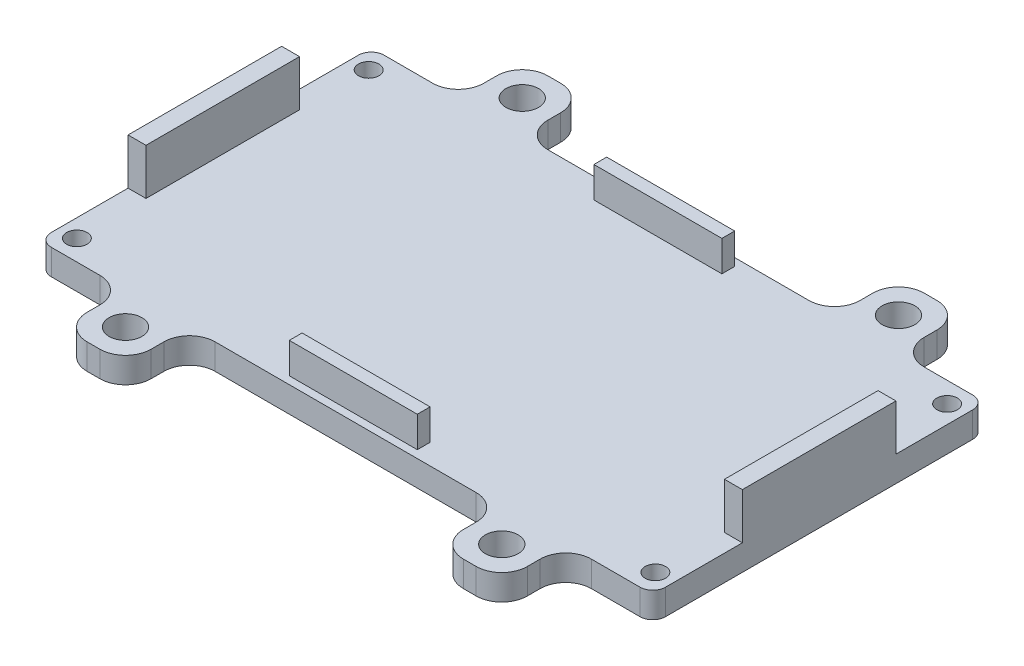
SolidWorks part; units mm, degrees
ref_plane "Front" through (0, 0, 0) normal (0, 0, 1) x (1, 0, 0)
ref_plane "Top" through (0, 0, 0) normal (0, 1, 0) x (1, 0, 0)
ref_plane "Right" through (0, 0, 0) normal (1, 0, 0) x (0, 0, -1)
sketch "草图1" plane through (0, 0, 0) normal (0, 1, 0) x (1, 0, 0)
  line L1 (-60, -32.5) -> (60, -32.5)
  line L2 (-60, -32.5) -> (-60, 32.5)
  line L3 (-60, 32.5) -> (60, 32.5)
  line L4 (60, -32.5) -> (60, 32.5)
  line L5 (-60, -32.5) -> (60, 32.5) construction
  line L6 (-60, 32.5) -> (60, -32.5) construction
  point P0 (0, 0)
  dimension "D1" = 120
  dimension "D2" = 65
extrude "凸台-拉伸1" add sketch "草图1" along normal blind 5
sketch "草图2" plane through (0, 5, 0) normal (0, 1, 0) x (1, 0, 0)
  line L0 (60, 32.5) -> (-60, 32.5) construction
  line L1 (-43, 32.5) -> (-30.5, 32.5)
  line L2 (-43, 32.5) -> (-43, 45)
  line L3 (-43, 45) -> (-30.5, 45)
  line L4 (-30.5, 32.5) -> (-30.5, 45)
  line L5 (-60, 32.5) -> (-60, -32.5) construction
  line L6 (0, 51.1348) -> (0, -43.6514) construction
  line L7 (-74.3344, 0) -> (82.9175, 0) construction
  line L8 (30.5, 32.5) -> (30.5, 45)
  line L9 (43, 32.5) -> (30.5, 32.5)
  line L10 (43, 45) -> (30.5, 45)
  line L11 (43, 32.5) -> (43, 45)
  line L12 (43, -32.5) -> (43, -45)
  line L13 (43, -45) -> (30.5, -45)
  line L14 (43, -32.5) -> (30.5, -32.5)
  line L15 (30.5, -32.5) -> (30.5, -45)
  line L16 (-30.5, -32.5) -> (-30.5, -45)
  line L17 (-43, -45) -> (-30.5, -45)
  line L18 (-43, -32.5) -> (-43, -45)
  line L19 (-43, -32.5) -> (-30.5, -32.5)
  dimension "D1" = 12.5
  dimension "D2" = 12.5
  dimension "D3" = 17
extrude "凸台-拉伸2" add sketch "草图2" against normal blind 5
sketch "草图3" plane through (0, 5, 0) normal (0, 1, 0) x (1, 0, 0)
  line L0 (0, 45.0986) -> (0, -48.8841) construction
  line L1 (-75.3167, 0) -> (82.8875, 0) construction
  line L2 (-30.5, 45) -> (-43, 45) construction
  line L3 (-43, 45) -> (-43, 32.5) construction
  circle A0 centre (-36.75, 38.75) radius 3.2
  circle A1 centre (36.75, 38.75) radius 3.2
  circle A2 centre (36.75, -38.75) radius 3.2
  circle A3 centre (-36.75, -38.75) radius 3.2
  dimension "D1" = 6.4
  dimension "D2" = 6.25
  dimension "D3" = 6.25
extrude "切除-拉伸1" cut sketch "草图3" against normal blind 5
sketch "草图4" plane through (0, 5, 0) normal (0, 1, 0) x (1, 0, 0)
  line L0 (-89.438, 0) -> (96.0594, 0) construction
  line L1 (-60, 32.5) -> (-60, -32.5) construction
  line L2 (-60, -15) -> (-56.5, -15)
  line L3 (-60, -15) -> (-60, 15)
  line L4 (-60, 15) -> (-56.5, 15)
  line L5 (-56.5, -15) -> (-56.5, 15)
  line L6 (-60, -15) -> (-56.5, 15) construction
  line L7 (-60, 15) -> (-56.5, -15) construction
  line L8 (0, 76.1686) -> (0, -94.3454) construction
  line L9 (60, 15) -> (56.5, -15) construction
  line L10 (60, -15) -> (56.5, 15) construction
  line L11 (89.438, 0) -> (-96.0594, 0) construction
  line L12 (56.5, -15) -> (56.5, 15)
  line L13 (60, 15) -> (56.5, 15)
  line L14 (60, -15) -> (60, 15)
  line L15 (60, -15) -> (56.5, -15)
  point P3 (-58.25, 0)
  point P18 (58.25, 0)
  dimension "D1" = 30
  dimension "D2" = 3.5
extrude "凸台-拉伸3" add sketch "草图4" along normal blind 9
fillet "圆角1" radius 5 16 edges at (43, 2.5, -32.5) (30.5, 2.5, -32.5) (30.5, 2.5, -45) (-30.5, 2.5, -32.5) (-43, 2.5, 32.5) (30.5, 2.5, 32.5) (43, 2.5, -45) (-30.5, 2.5, -45) (30.5, 2.5, 45) (-43, 2.5, 45) (-30.5, 2.5, 45) (-30.5, 2.5, 32.5) (43, 2.5, 45) (43, 2.5, 32.5) (-43, 2.5, -45) (-43, 2.5, -32.5)
fillet "圆角2" radius 2.5 4 edges at (-60, 2.5, 32.5) (-60, 2.5, -32.5) (60, 2.5, -32.5) (60, 2.5, 32.5)
sketch "草图5" plane through (0, 5, 0) normal (0, 1, 0) x (1, 0, 0)
  line L0 (0, 46.8475) -> (0, -51.1599) construction
  line L1 (25.5, 32.5) -> (-25.5, 32.5) construction
  line L2 (-12.5, 31) -> (12.5, 31)
  line L3 (-12.5, 31) -> (-12.5, 28.5)
  line L4 (-12.5, 28.5) -> (12.5, 28.5)
  line L5 (12.5, 31) -> (12.5, 28.5)
  line L6 (-12.5, 31) -> (12.5, 28.5) construction
  line L7 (-12.5, 28.5) -> (12.5, 31) construction
  line L8 (-12.5, -31) -> (12.5, -31)
  line L9 (-12.5, -31) -> (-12.5, -28.5)
  line L10 (-12.5, -28.5) -> (12.5, -28.5)
  line L11 (12.5, -31) -> (12.5, -28.5)
  line L12 (-12.5, -31) -> (12.5, -28.5) construction
  line L13 (-12.5, -28.5) -> (12.5, -31) construction
  point P3 (0, 29.75)
  point P8 (0, -29.75)
  dimension "D1" = 57
  dimension "D2" = 2.5
  dimension "D3" = 2.5
  dimension "D4" = 1.5
  dimension "D5" = 25
  dimension "D6" = 25
extrude "凸台-拉伸4" add sketch "草图5" along normal blind 6
sketch "草图6" plane through (0, 5, 0) normal (0, 1, 0) x (1, 0, 0)
  line L0 (0, 45.6422) -> (0, -48.9164) construction
  line L1 (-82.2477, 0) -> (88.927, 0) construction
  line L2 (12.5, 28.5) -> (-35.57, 28.5) construction
  line L4 (-56.5, -15) -> (-56.5, 43.8087) construction
  circle A0 centre (-56.5, 28.5) radius 2
  circle A1 centre (56.5, 28.5) radius 2
  circle A2 centre (56.5, -28.5) radius 2
  circle A3 centre (-56.5, -28.5) radius 2
  point P13 (0, 0)
  dimension "D1" = 4
extrude "切除-拉伸2" cut sketch "草图6" against normal blind 10
